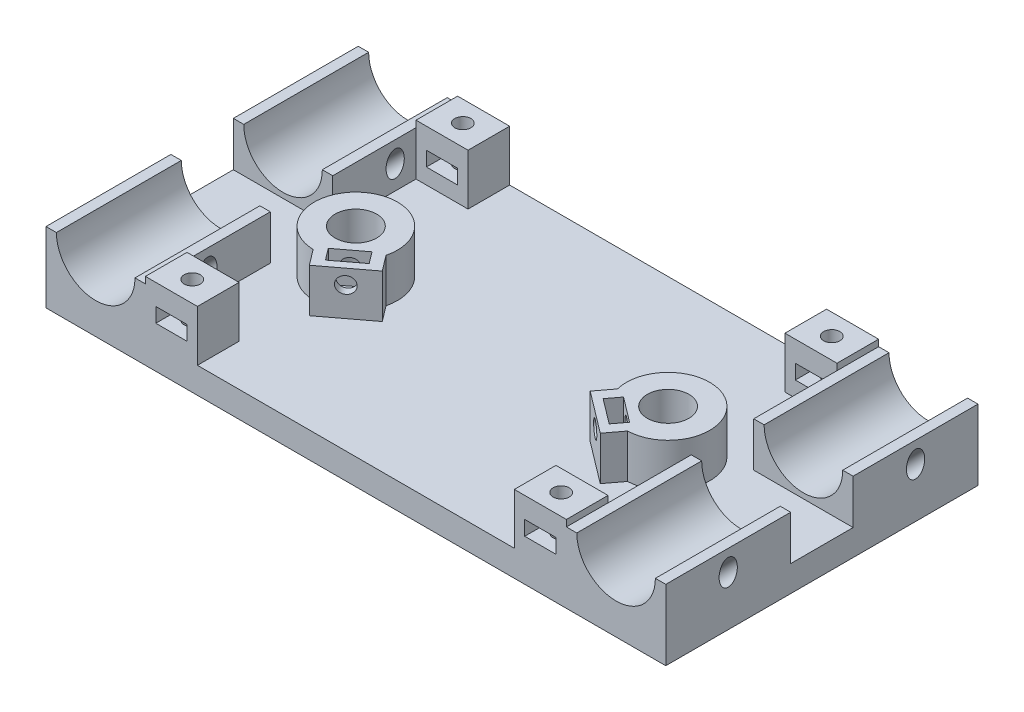
SolidWorks part; units mm, degrees
ref_plane "Front Plane" through (0, 0, 0) normal (0, 0, 1) x (1, 0, 0)
ref_plane "Top Plane" through (0, 0, 0) normal (0, 1, 0) x (1, 0, 0)
ref_plane "Right Plane" through (0, 0, 0) normal (1, 0, 0) x (0, 0, -1)
sketch "Sketch1" plane through (0, 0, 0) normal (0, 1, 0) x (1, 0, 0)
  line L1 (-59.55, 30) -> (59.55, 30)
  line L2 (-59.55, 30) -> (-59.55, -30)
  line L3 (-59.55, -30) -> (59.55, -30)
  line L4 (59.55, 30) -> (59.55, -30)
  dimension "D1" = 60
  dimension "D2" = 119.1
  dimension "D3" = 59.55
  dimension "D4" = 30
extrude "Boss-Extrude1" add sketch "Sketch1" along normal blind 5
sketch "Sketch2" plane through (0, 0, 30) normal (0, 0, 1) x (1, 0, 0)
  line L0 (-59.55, 5) -> (59.55, 5) construction
  line L1 (-59.55, 5) -> (-40.45, 5)
  line L2 (-59.55, 5) -> (-59.55, 13.55)
  line L3 (-59.55, 13.55) -> (-40.45, 13.55)
  line L4 (-40.45, 5) -> (-40.45, 13.55)
  circle A0 centre (-50, 13.55) radius 7.55
  line M3 (59.55, 5) -> (-59.55, 5)
  dimension "D3" = 15.1
  dimension "D1" = 19.1
  dimension "D2" = 8.55
  dimension "D4" = 50
extrude "Boss-Extrude2" add sketch "Sketch2" against normal blind 24 contours A0 L3 L2 L4 M3
mirror "Mirror1" about plane through (0, 0, 0) normal (0, 0, 1) of "Boss-Extrude2"
mirror "Mirror2" about plane through (0, 0, 0) normal (1, 0, 0) of "Mirror1", "Boss-Extrude2"
ref_plane "Plane1" through (-50, 0, 0) normal (-1, 0, 0) x (0, 0, 1)
ref_plane "Plane2" through (-32.275, 32.275, 0) normal (-0.7071, 0.7071, 0) x (0.7071, 0.7071, 0)
sketch "Sketch3" plane through (-32.275, 32.275, 0) normal (-0.7071, 0.7071, 0) x (0.7071, 0.7071, 0)
  circle A0 centre (-35.3553, -18) radius 1.75
  dimension "D1" = 3.5
extrude "Cut-Extrude1" cut sketch "Sketch3" against normal through all both and the other way through all
mirror "Mirror3" about plane through (-50, 0, 0) normal (-1, 0, 0) of "Cut-Extrude1"
mirror "Mirror4" about plane through (0, 0, 0) normal (0, 0, 1) of "Mirror3", "Cut-Extrude1"
mirror "Mirror5" about plane through (0, 0, 0) normal (1, 0, 0) of "Mirror4", "Cut-Extrude1", "Mirror3"
sketch "Sketch4" plane through (0, 5, 0) normal (0, 1, 0) x (1, 0, 0)
  line L0 (-27.9509, -10.991) -> (-30.2173, -7.997)
  line L1 (-27.9509, -10.991) -> (-19.9778, -4.9553)
  line L2 (-19.9778, -4.9553) -> (-22.2442, -1.9614)
  circle A0 centre (-30, 0) radius 4
  circle A1 centre (30, 0) radius 4
  circle A2 centre (-30, 0) radius 8
  circle A3 centre (30, 0) radius 8
  dimension "D1" = 8
  dimension "D2" = 8
  dimension "D5" = 16
  dimension "D6" = 16
  dimension "D3" = 30
  dimension "D4" = 30
  dimension "D7" = 10
  dimension "D8" = 10
  dimension "D9" = 5
extrude "Boss-Extrude3" add sketch "Sketch4" along normal blind 8.4
sketch "Sketch6" plane through (0, 13.4, 0) normal (0, 1, 0) x (1, 0, 0)
  line L1 (-28.9516, -6.3554) -> (-24.1677, -2.734)
  line L2 (-28.9516, -6.3554) -> (-27.2617, -8.5879)
  line L3 (-27.2617, -8.5879) -> (-22.4778, -4.9665)
  line L4 (-24.1677, -2.734) -> (-22.4778, -4.9665)
  line L5 (-28.9516, -6.3554) -> (-22.4778, -4.9665) construction
  line L6 (-27.2617, -8.5879) -> (-24.1677, -2.734) construction
  line L7 (-19.9778, -4.9553) -> (-22.2442, -1.9614) construction
  line L8 (-27.9509, -10.991) -> (-19.9778, -4.9553) construction
  line L9 (-27.9509, -10.991) -> (-19.9778, -4.9553) construction
  line L10 (-27.9509, -10.991) -> (-30.2173, -7.997) construction
  point P0 (-25.7147, -5.6609)
  dimension "D1" = 2.8
  dimension "D2" = 6
  dimension "D3" = 1.5
  dimension "D4" = 2
extrude "Cut-Extrude3" cut sketch "Sketch6" against normal blind 6
sketch "Sketch7" plane through (-4.893, 0, -6.4637) normal (0.6036, 0, 0.7973) x (0.7973, 0, -0.6036)
  line L0 (-28.9195, 13.4) -> (-18.9195, 13.4) construction
  line L1 (-28.9195, 13.4) -> (-28.9195, 5) construction
  circle A0 centre (-23.9195, 10.6) radius 1.5614
  dimension "D1" = 2.8
  dimension "D2" = 5
extrude "Cut-Extrude4" cut sketch "Sketch7" against normal blind 8
mirror "Mirror7" about plane through (0, 0, 0) normal (1, 0, 0) of "Cut-Extrude3", "Boss-Extrude3", "Cut-Extrude4"
sketch "Sketch8" plane through (0, 5, 0) normal (0, 1, 0) x (1, 0, 0)
  circle A0 centre (-30, 0) radius 4
  circle A1 centre (30, 0) radius 4
extrude "Cut-Extrude5" cut sketch "Sketch8" against normal blind 8
sketch "Sketch9" plane through (0, 0, 30) normal (0, 0, 1) x (1, 0, 0)
  line L1 (-40.45, 5) -> (-30.45, 5)
  line L2 (-40.45, 5) -> (-40.45, 14.8)
  line L3 (-40.45, 14.8) -> (-30.45, 14.8)
  line L4 (-30.45, 5) -> (-30.45, 14.8)
  line L5 (-38.45, 8) -> (-32.45, 8)
  line L6 (-38.45, 8) -> (-38.45, 10.8)
  line L7 (-38.45, 10.8) -> (-32.45, 10.8)
  line L8 (-32.45, 8) -> (-32.45, 10.8)
  line M7 (40.45, 5) -> (-40.45, 5)
  line M8 (-40.45, 5) -> (-40.45, 13.55)
  dimension "D1" = 2.8
  dimension "D2" = 6
  dimension "D3" = 2
  dimension "D4" = 2
  dimension "D5" = 4
  dimension "D6" = 3
extrude "Boss-Extrude4" add sketch "Sketch9" against normal blind 8 contours L8 L4 L3 L6 L7 M7 M8
mirror "Mirror8" about plane through (0, 0, 0) normal (1, 0, 0) of "Boss-Extrude4"
mirror "Mirror9" about plane through (0, 0, 0) normal (0, 0, 1) of "Mirror8", "Boss-Extrude4"
sketch "Sketch10" plane through (0, 14.8, 0) normal (0, 1, 0) x (1, 0, 0)
  line L0 (-40.45, -22) -> (-30.45, -22) construction
  line L1 (-30.45, -22) -> (-30.45, -30) construction
  line L2 (30.45, -22) -> (30.45, -30) construction
  line L4 (40.45, -22) -> (30.45, -22) construction
  line L5 (40.45, 22) -> (30.45, 22) construction
  line L6 (30.45, 22) -> (30.45, 30) construction
  line L7 (-30.45, 22) -> (-30.45, 30) construction
  line L8 (-40.45, 22) -> (-30.45, 22) construction
  circle A0 centre (-35.45, 26) radius 1.55
  circle A1 centre (35.45, 26) radius 1.55
  circle A2 centre (35.45, -26) radius 1.55
  circle A3 centre (-35.45, -26) radius 1.55
  point P16 (32.4396, -22.4284)
  point P21 (-30.45, 26)
  dimension "D1" = 3.1
  dimension "D2" = 4
  dimension "D3" = 5
  dimension "D4" = 5
  dimension "D5" = 4
  dimension "D6" = 4
  dimension "D7" = 5
  dimension "D8" = 5
  dimension "D9" = 4
extrude "Cut-Extrude6" cut sketch "Sketch10" against normal through all
